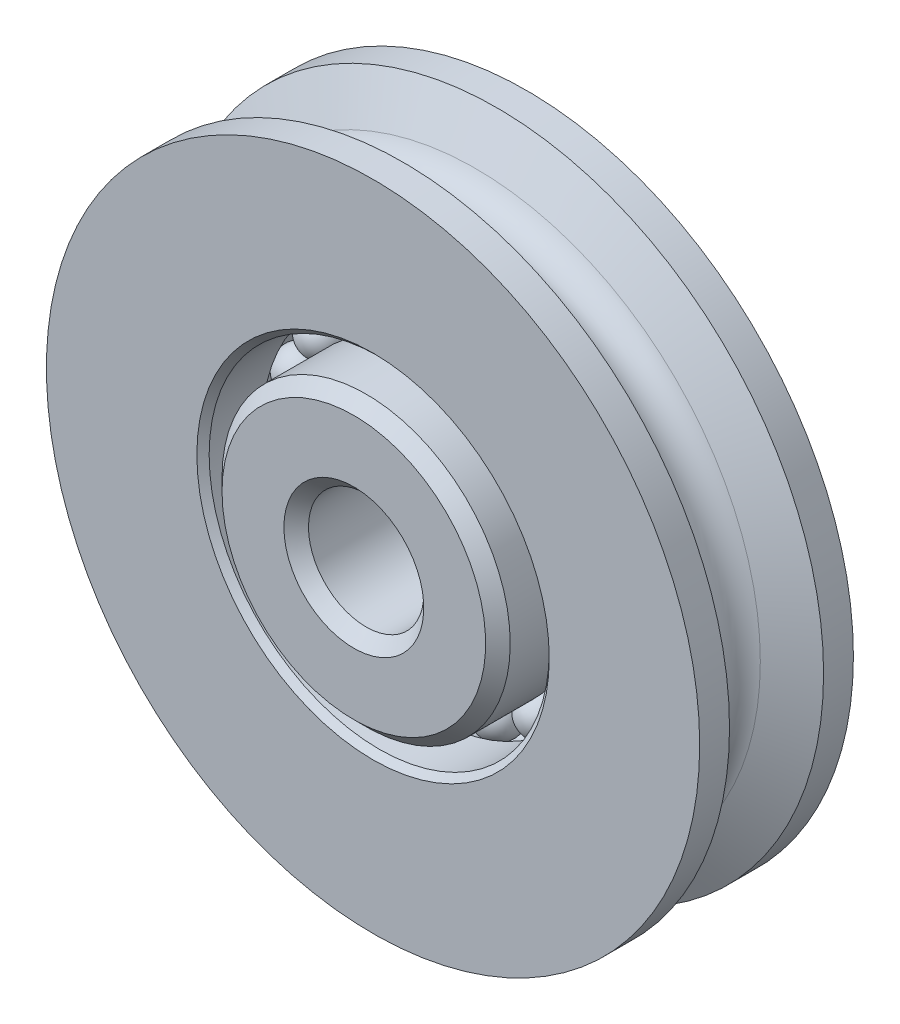
SolidWorks part; units mm, degrees
ref_plane "Front" through (0, 0, 0) normal (0, 0, 1) x (1, 0, 0)
ref_plane "Top" through (0, 0, 0) normal (0, 1, 0) x (1, 0, 0)
ref_plane "Right" through (0, 0, 0) normal (1, 0, 0) x (0, 0, -1)
sketch "Sketch1" plane through (0, 0, 0) normal (1, 0, 0) x (0, 0, -1)
  line L0 (1.9431, 13.4937) -> (3.175, 13.4937)
  line L1 (-1.9431, 13.4937) -> (-3.175, 13.4937)
  line L2 (-1.9431, 13.4937) -> (-1.0608, 11.7625)
  line L3 (0.7144, 7.0247) -> (3.175, 7.0247)
  line L4 (3.9688, 2.3812) -> (-3.9688, 2.3812)
  line L5 (-0.7144, 5.9531) -> (-3.9688, 5.9531)
  line L6 (1.9431, 13.4937) -> (1.0608, 11.7625)
  line L8 (-3.9688, 0) -> (3.9688, 0) construction
  line L10 (3.175, 13.4937) -> (3.175, 7.0247)
  line L13 (-3.9688, 5.9531) -> (-3.9688, 2.3812)
  line L14 (0, 11.1125) -> (0, -11.1125) construction
  line L16 (3.9688, 5.9531) -> (3.9688, 2.3812)
  line L17 (-3.175, 13.4937) -> (-3.175, -13.4937) construction
  line L18 (-3.175, 7.0247) -> (-0.7144, 7.0247)
  line L20 (3.9688, 5.9531) -> (0.7144, 5.9531)
  line L21 (-3.175, 7.0247) -> (-3.175, 13.4937)
  arc A0 (-1.0608, 11.7625) -> (1.0608, 11.7625) centre (0, 12.3031) ccw
  circle A1 centre (0, 12.3031) radius 1.1906 construction
  circle A2 centre (0, 0) radius 2.3813 construction
  circle A3 centre (0, 0) radius 5.9531 construction
  arc A4 (-0.7144, 5.9531) -> (0.7144, 5.9531) centre (0, 6.4889) ccw
  circle A5 centre (0, -12.3031) radius 1.1906 construction
  arc A6 (0.7144, 7.0247) -> (-0.7144, 7.0247) centre (0, 6.4889) ccw
  point P28 (-3.175, 0)
  dimension "Rope Dia" = 2.3813
  dimension "Shaft Dia" = 4.7625
  dimension "D1" = 11.9063
  dimension "D2" = 1.7859
  dimension "Wd" = 7.9375
  dimension "D8" = 1.2319
  dimension "Groove Dia" = 22.225
  dimension "OD" = 26.9875
  dimension "w Wd" = 6.35
  dimension "D3" = 1.0716
revolve "Revolve1" add sketch "Sketch1" angle 360 about L8
sketch "Sketch2" plane through (0, 0, 0) normal (1, 0, 0) x (0, 0, -1)
  line L0 (0, 11.1125) -> (0, -11.1125) construction
  line L1 (0, 7.3819) -> (0, 5.5959)
  arc A0 (0.7144, 7.0247) -> (-0.7144, 7.0247) centre (0, 6.4889) ccw construction
  arc A1 (0, 5.5959) -> (0, 7.3819) centre (0, 6.4889) ccw
revolve "Revolve2" add sketch "Sketch2" angle 360 about L1
pattern_circular "CirPattern1" count 20 over 360 about axis through (0, 0, 0) along (0, 0, 1) of bodies 117
chamfer "Chamfer1" distance 0.508 angle 45 4 edges at (2.3812, 0, -3.9688) (5.9531, 0, -3.9688) (5.9531, 0, 3.9688) (2.3812, 0, 3.9688)
chamfer "Chamfer2" distance 0.254 angle 45 2 edges at (7.0247, 0, -3.175) (7.0247, 0, 3.175)
equation "\"D1@Sketch1\" = \"Shaft Dia@Sketch1\" * 2.5"
equation "\"D2@Sketch1\" = \"Rope Dia@Sketch1\" * .75"
equation "\"D3@Sketch1\" = \"D2@Sketch1\" * .6"
